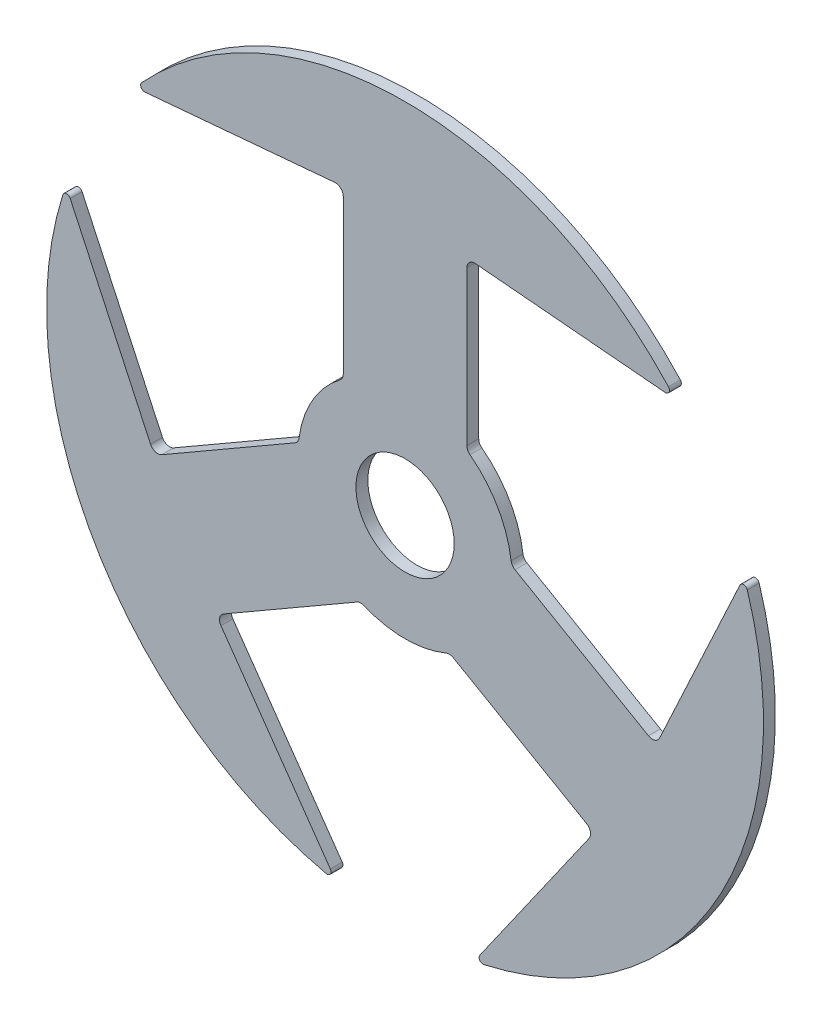
SolidWorks part; units mm, degrees
ref_plane "Front Plane" through (0, 0, 0) normal (0, 0, 1) x (1, 0, 0)
ref_plane "Top Plane" through (0, 0, 0) normal (0, 1, 0) x (1, 0, 0)
ref_plane "Right Plane" through (0, 0, 0) normal (1, 0, 0) x (0, 0, -1)
sketch "Sketch1" plane through (0, 0, 0) normal (0, 0, 1) x (1, 0, 0)
  line L3 (1.9812, 2.9272) -> (1.9812, 7.8665)
  line L4 (-1.9812, 2.9272) -> (-1.9812, 7.8665)
  line L5 (-2.2575, 8.1195) -> (-8.3407, 7.5834)
  line L6 (2.2575, 8.1195) -> (8.3407, 7.5834)
  line L7 (8.1605, -2.1047) -> (10.7378, 3.4316)
  line L8 (3.5256, 0.2522) -> (7.8032, -2.2175)
  line L9 (1.5444, -3.1794) -> (5.822, -5.649)
  line L10 (5.903, -6.0148) -> (2.3971, -11.015)
  line L11 (-5.903, -6.0148) -> (-2.3971, -11.015)
  line L12 (-1.5444, -3.1794) -> (-5.822, -5.649)
  line L13 (-3.5256, 0.2522) -> (-7.8032, -2.2175)
  line L14 (-8.1605, -2.1047) -> (-10.7378, 3.4316)
  arc A0 (-10.9742, 3.4157) -> (-2.529, -11.2118) centre (0, 0) ccw
  arc A1 (-2.081, 2.7253) -> (-3.4007, 0.4396) centre (0, 0) ccw
  arc A2 (2.081, 2.7253) -> (1.9812, 2.9272) centre (2.2352, 2.9272) cw
  arc A3 (-1.9812, 2.9272) -> (-2.081, 2.7253) centre (-2.2352, 2.9272) cw
  arc A4 (-1.3197, -3.1649) -> (1.3197, -3.1649) centre (0, 0) ccw
  arc A5 (3.4007, 0.4396) -> (2.081, 2.7253) centre (0, 0) ccw
  arc A6 (-3.4007, 0.4396) -> (-3.5256, 0.2522) centre (-3.6526, 0.4722) cw
  arc A7 (3.4007, 0.4396) -> (3.5256, 0.2522) centre (3.6526, 0.4722) ccw
  arc A8 (1.3197, -3.1649) -> (1.5444, -3.1794) centre (1.4174, -3.3993) cw
  arc A9 (-1.5444, -3.1794) -> (-1.3197, -3.1649) centre (-1.4174, -3.3993) cw
  arc A10 (2.529, -11.2118) -> (10.9742, 3.4157) centre (0, 0) ccw
  arc A11 (8.4452, 7.7961) -> (-8.4452, 7.7961) centre (0, 0) ccw
  circle A12 centre (0, 0) radius 1.5748
  arc A13 (2.529, -11.2118) -> (2.3971, -11.015) centre (2.5011, -11.0879) cw
  arc A14 (-2.529, -11.2118) -> (-2.3971, -11.015) centre (-2.5011, -11.0879) ccw
  arc A15 (-10.9742, 3.4157) -> (-10.7378, 3.4316) centre (-10.853, 3.378) cw
  arc A16 (10.9742, 3.4157) -> (10.7378, 3.4316) centre (10.853, 3.378) ccw
  arc A17 (8.4452, 7.7961) -> (8.3407, 7.5834) centre (8.3519, 7.7099) cw
  arc A18 (-8.3407, 7.5834) -> (-8.4452, 7.7961) centre (-8.3519, 7.7099) cw
  arc A19 (-8.1605, -2.1047) -> (-7.8032, -2.2175) centre (-7.9302, -1.9975) ccw
  arc A20 (-5.903, -6.0148) -> (-5.822, -5.649) centre (-5.695, -5.869) cw
  arc A21 (5.903, -6.0148) -> (5.822, -5.649) centre (5.695, -5.869) ccw
  arc A22 (8.1605, -2.1047) -> (7.8032, -2.2175) centre (7.9302, -1.9975) cw
  arc A23 (1.9812, 7.8665) -> (2.2575, 8.1195) centre (2.2352, 7.8665) cw
  arc A24 (-1.9812, 7.8665) -> (-2.2575, 8.1195) centre (-2.2352, 7.8665) ccw
  point P34 (0, 0)
  point P36 (3.4144, 0.3164)
  point P39 (1.4332, -3.1151)
  point P42 (-1.4332, -3.1151)
  dimension "D1" = 22.987
  dimension "D2" = 6.858
  dimension "D3" = 3.1496
  dimension "D6" = 0.254
  dimension "D5" = 0.127
  dimension "D7" = 0.254
  dimension "D4" = 3
extrude "Boss-Extrude1" add sketch "Sketch1" along normal blind 0.381
